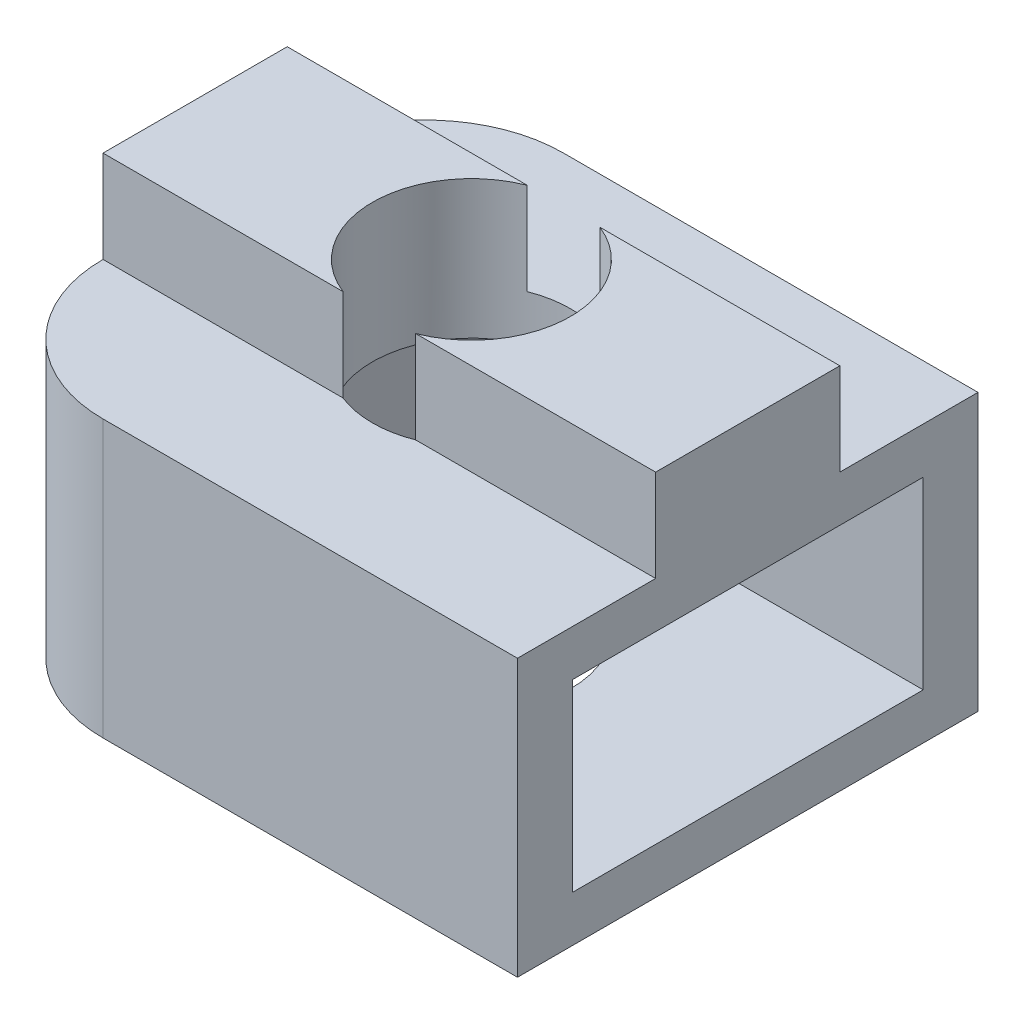
SolidWorks part; units mm, degrees
ref_plane "Plan de face" through (0, 0, 0) normal (0, 0, 1) x (1, 0, 0)
ref_plane "Plan de dessus" through (0, 0, 0) normal (0, 1, 0) x (1, 0, 0)
ref_plane "Plan de droite" through (0, 0, 0) normal (1, 0, 0) x (0, 0, -1)
sketch "Sketch1" plane through (0, 0, 0) normal (0, 1, 0) x (1, 0, 0)
  line L1 (-6, 5) -> (6, 5)
  line L2 (-6, 5) -> (-6, -5)
  line L3 (-6, -5) -> (6, -5)
  line L4 (6, 5) -> (6, -5)
  line L5 (-6, 5) -> (6, -5) construction
  line L6 (-6, -5) -> (6, 5) construction
  point P0 (0, 0)
  dimension "D1" = 10
  dimension "D2" = 12
extrude "Boss-Extrude1" add sketch "Sketch1" along normal blind 1 contours L2 L3 L4 L1
sketch "Sketch2" plane through (0, 1, 0) normal (0, 1, 0) x (1, 0, 0)
  line L0 (2.2, -3.8105) -> (6, -3.8105)
  line L2 (2.2, 3.8105) -> (-2.2, 3.8105)
  line L3 (-2.2, 3.8105) -> (-4.4, 0)
  line L4 (-4.4, 0) -> (-2.2, -3.8105)
  line L5 (-2.2, -3.8105) -> (2.2, -3.8105)
  line L7 (-6, -5) -> (6, -5)
  line L8 (-6, -5) -> (-6, 5)
  line L9 (-6, 5) -> (6, 5)
  line L10 (6, -5) -> (6, -3.8105)
  line L11 (2.2, 3.8105) -> (6, 3.8105)
  line L12 (6, 3.8105) -> (6, 5)
  line L13 (2.2, -3.8105) -> (3.3, -1.9053) [skipped]
  line L14 (3.3, 1.9053) -> (2.2, 3.8105) [skipped]
  line L15 (0, 3.8105) -> (0, -3.8105) construction
  line L16 (-4.4, 0) -> (0, 0) construction
  line L17 (0, 0) -> (4.4, 0) construction
  line L18 (4.4, 0) -> (2.2, 3.8105) construction
  line L19 (4.4, 0) -> (2.2, -3.8105) construction
  arc A0 (0, 3.8105) -> (0, -3.8105) centre (0, 0) ccw construction
  dimension "D1" = 8.8
extrude "Boss-Extrude2" add sketch "Sketch2" along normal blind 4
sketch "Sketch3" plane through (0, 5, 0) normal (0, 1, 0) x (1, 0, 0)
  line L1 (-6, 5) -> (6, 5)
  line L2 (-6, 5) -> (-6, -5)
  line L3 (-6, -5) -> (6, -5)
  line L4 (6, 5) -> (6, -5)
extrude "Boss-Extrude3" add sketch "Sketch3" along normal blind 1
sketch "Sketch5" plane through (0, 6, 0) normal (0, 1, 0) x (1, 0, 0)
  line L0 (6, -5) -> (6, 5) construction
  line L1 (-6, 2) -> (6, 2)
  line L2 (-6, 2) -> (-6, -2)
  line L3 (-6, -2) -> (6, -2)
  line L4 (6, 2) -> (6, -2)
  line L5 (-6, 2) -> (6, -2) construction
  line L6 (-6, -2) -> (6, 2) construction
  point P0 (0, 0)
  dimension "D1" = 4
extrude "Boss-Extrude4" add sketch "Sketch5" along normal blind 2 contours L3 L4 L1 L2
sketch "Sketch4" plane through (0, 6, 0) normal (0, 1, 0) x (1, 0, 0)
  circle A0 centre (0, 0) radius 2.15
  dimension "D1" = 4.3
extrude "Cut-Extrude1" cut sketch "Sketch4" against normal through all both and the other way through all
fillet "Fillet1" radius 3 2 edges at (-6, 3, 5) (-6, 3, -5)
